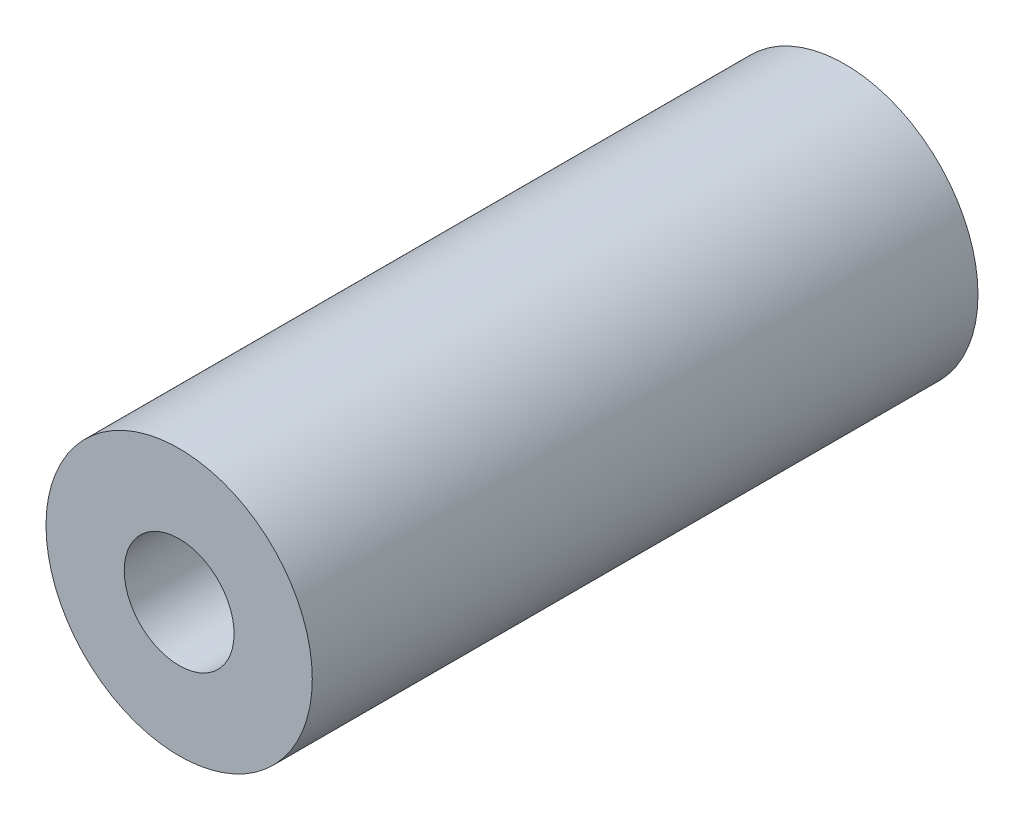
SolidWorks part; units mm, degrees
ref_plane "Front Plane" through (0, 0, 0) normal (0, 0, 1) x (1, 0, 0)
ref_plane "Top Plane" through (0, 0, 0) normal (0, 1, 0) x (1, 0, 0)
ref_plane "Right Plane" through (0, 0, 0) normal (1, 0, 0) x (0, 0, -1)
sketch "Sketch1" plane through (0, 0, 0) normal (0, 0, 1) x (1, 0, 0)
  circle A0 centre (0, 0) radius 4
  dimension "D1" = 8
extrude "Boss-Extrude1" add sketch "Sketch1" along normal blind 20
hole_wizard "Tap Drill for M4x0.7 Tap1" positions "Sketch2" profile "Sketch3" hole size "M4x0.7" standard "ANSI Metric" end condition up to next
sketch "Sketch2" plane through (0, 0, 0) normal (0, 0, -1) x (-1, 0, 0)
  point P0 (0, 0)
sketch "Sketch3" plane through (0, 0, 0) normal (1, 0, 0) x (0, 1, 0)
  line L0 (0, 0) -> (0, 20)
  line L1 (0, 20) -> (1.65, 20)
  line L2 (1.65, 20) -> (1.65, 0)
  line L5 (1.65, 0) -> (0, 0)
  line L11 (0, -6.35) -> (0, 107.95) construction
  dimension "Thru Hole Dia." = 3.3
  dimension "Thru Hole Depth" = 20
